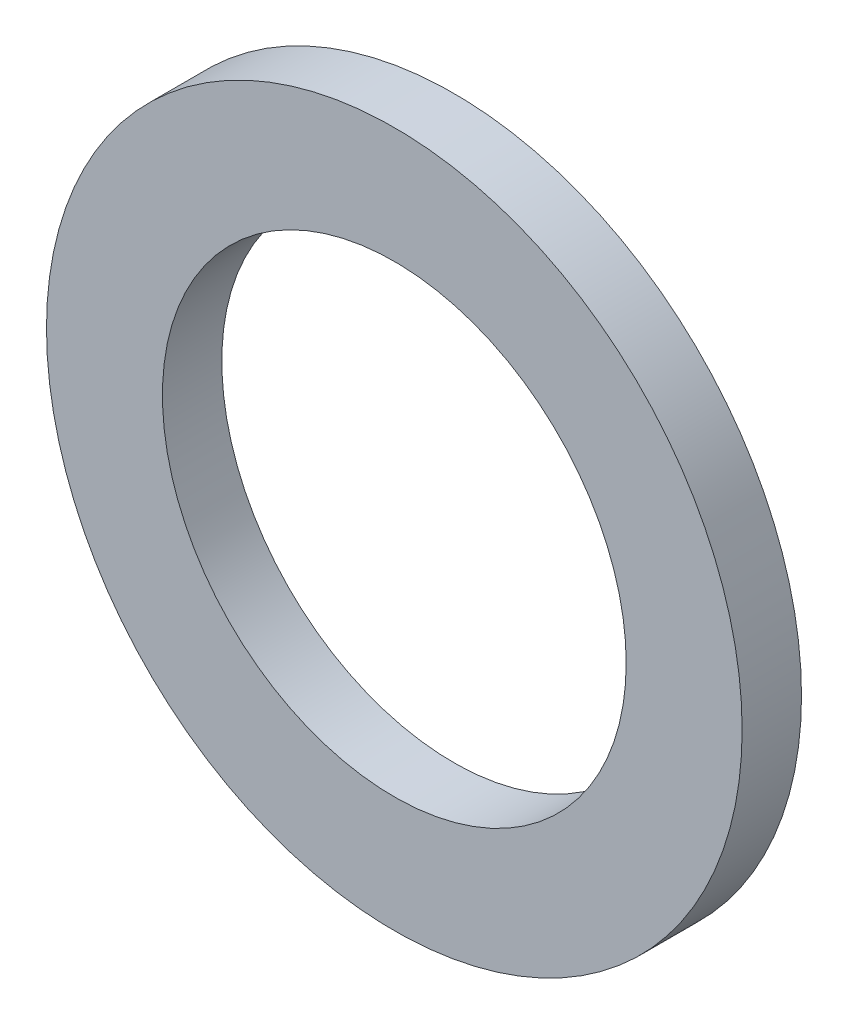
SolidWorks part; units mm, degrees
material "Plain Carbon Steel"
ref_plane "Front Plane" through (0, 0, 0) normal (0, 0, 1) x (1, 0, 0)
ref_plane "Top Plane" through (0, 0, 0) normal (0, 1, 0) x (1, 0, 0)
ref_plane "Right Plane" through (0, 0, 0) normal (1, 0, 0) x (0, 0, -1)
sketch "Sketch1" plane through (0, 0, 0) normal (0, 0, 1) x (1, 0, 0)
  circle A0 centre (0, 0) radius 4.7625
  circle A1 centre (0, 0) radius 3.175
  dimension "D1" = 6.35
  dimension "D2" = 9.525
extrude "Boss-Extrude1" add sketch "Sketch1" along normal blind 0.8128
